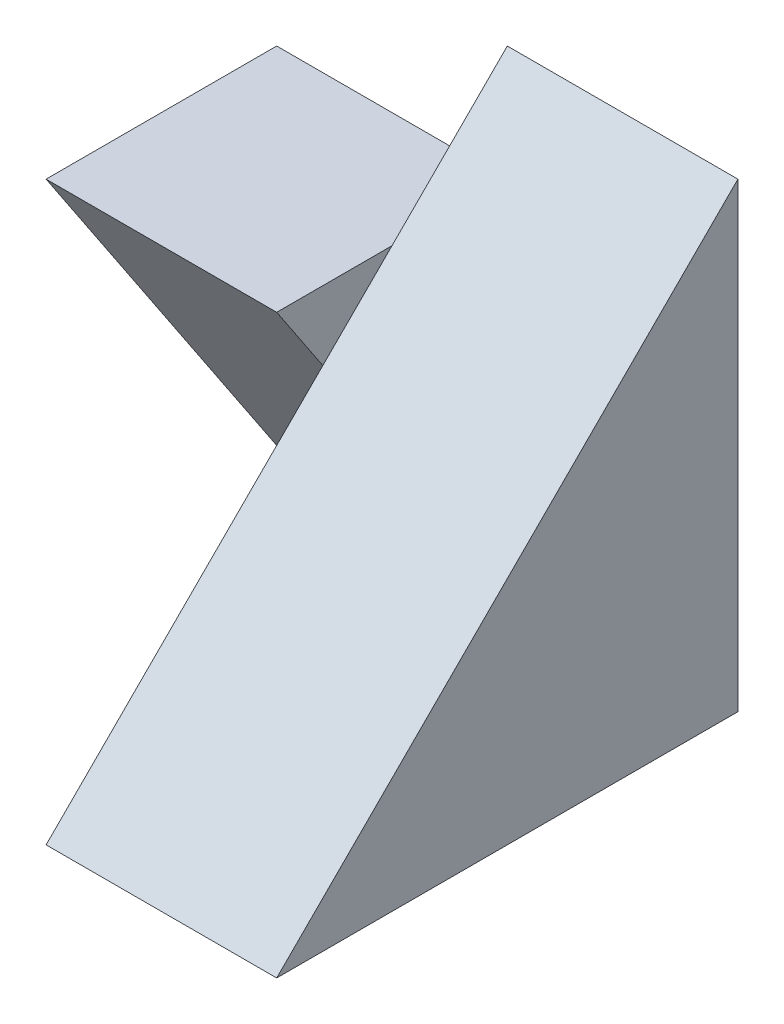
SolidWorks part; units mm, degrees
ref_plane "Front Plane" through (0, 0, 0) normal (0, 0, 1) x (1, 0, 0)
ref_plane "Top Plane" through (0, 0, 0) normal (0, 1, 0) x (1, 0, 0)
ref_plane "Right Plane" through (0, 0, 0) normal (1, 0, 0) x (0, 0, -1)
sketch "Sketch1" plane through (0, 0, 0) normal (1, 0, 0) x (0, 0, -1)
  line L1 (0, 0) -> (4, 0)
  line L2 (0, 0) -> (0, 4)
  line L3 (0, 4) -> (4, 4)
  line L4 (4, 0) -> (4, 4)
  dimension "D1" = 4
  dimension "D2" = 4
extrude "Boss-Extrude1" add sketch "Sketch1" along normal blind 2
sketch "Sketch2" plane through (0, 0, 0) normal (-1, 0, 0) x (0, 0, 1)
  line L1 (-4, 0) -> (-2, 0)
  line L2 (-4, 0) -> (-4, 3)
  line L3 (-4, 3) -> (-2, 3)
  line L4 (-2, 0) -> (-2, 3)
  dimension "D1" = 3
  dimension "D2" = 2
extrude "Boss-Extrude2" add sketch "Sketch2" along normal blind 2
sketch "Sketch3" plane through (-2, 0, 0) normal (-1, 0, 0) x (0, 0, 1)
  line L0 (-2, 3) -> (-4, 0)
  line L1 (-4, 0) -> (-4, 3)
  line L2 (-4, 3) -> (-2, 3)
  line M5 (-4, 0) -> (-2, 0)
  line M6 (-2, 0) -> (-2, 3)
extrude "Cut-Extrude1" cut sketch "Sketch3" against normal blind 2 contours L0 M6 M5
sketch "Sketch4" plane through (2, 0, 0) normal (1, 0, 0) x (0, 0, -1)
  line L0 (4, 4) -> (0, 0)
  line L1 (0, 0) -> (0, 4)
  line L2 (0, 4) -> (4, 4)
extrude "Cut-Extrude2" cut sketch "Sketch4" against normal blind 2
